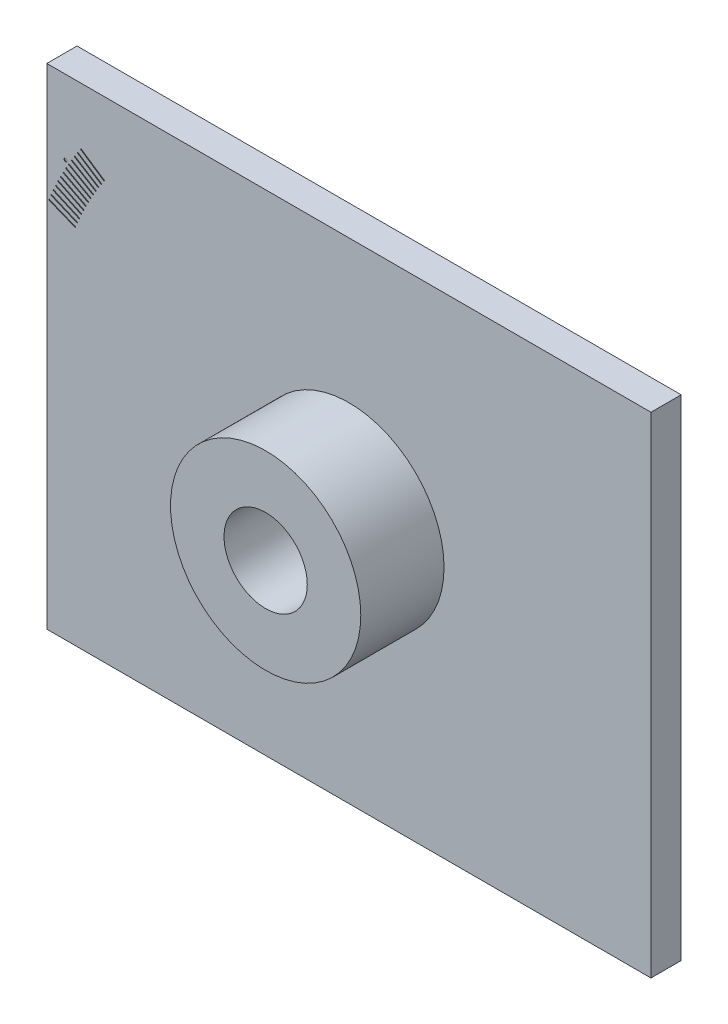
SolidWorks part; units mm, degrees
material "6063-T6"
ref_plane "Front Plane" through (0, 0, 0) normal (0, 0, 1) x (1, 0, 0)
ref_plane "Top Plane" through (0, 0, 0) normal (0, 1, 0) x (1, 0, 0)
ref_plane "Right Plane" through (0, 0, 0) normal (1, 0, 0) x (0, 0, -1)
sketch "Sketch1" plane through (0, 0, 0) normal (0, 0, 1) x (1, 0, 0)
  line L1 (-127, 100) -> (127, 100)
  line L2 (-127, 100) -> (-127, -106)
  line L3 (-127, -106) -> (127, -106)
  line L4 (127, 100) -> (127, -106)
  dimension "D1" = 127
  dimension "D2" = 127
  dimension "D3" = 100
  dimension "D4" = 106
extrude "Body" add sketch "Sketch1" along normal blind 12.7
sketch "Sketch2" plane through (0, 0, 12.7) normal (0, 0, 1) x (1, 0, 0)
  circle A0 centre (0, 0) radius 40
  dimension "D1" = 80
extrude "Spigot" add sketch "Sketch2" along normal blind 35
sketch "Sketch3" plane through (0, 0, 47.7) normal (0, 0, 1) x (1, 0, 0)
  circle A0 centre (0, 0) radius 17.5
  dimension "D1" = 35
extrude "Hole" cut sketch "Sketch3" against normal through all
sketch "Sketch4" plane through (0, 0, 12.7) normal (0, 0, 1) x (1, 0, 0)
  line L0 (0, 0) -> (-177.2977, 102.3629) construction
  line L1 (0, 0) -> (-190.234, 0) construction
  line L2 (0, 0) -> (-107.3872, 62)
  line L3 (-107.5122, 61.7835) -> (-107.2622, 62.2165)
  line L4 (-107.5122, 61.7835) -> (-117.9045, 67.7835)
  line L5 (-117.9045, 67.7835) -> (-117.6545, 68.2165)
  line L6 (-117.6545, 68.2165) -> (-107.2622, 62.2165)
  dimension "D1" = 30
  dimension "D2" = 124
  dimension "D3" = 0.5
  dimension "D4" = 12
extrude "Slit" cut sketch "Sketch4" against normal blind 0.25 contours L6 L5 L4 L3
sketch "Sketch5" plane through (0, 0, 12.7) normal (0, 0, 1) x (1, 0, 0)
  line L0 (0, 0) -> (-235.4142, 135.9165) construction
  line L1 (0, 0) -> (-227.8121, 0) construction
  dimension "D1" = 30
pattern_circular "Right Slits" count 5 every 1 about axis through (0, 0, 0) along (0, 0, 1) of "Slit"
pattern_circular "Left Slits" count 9 every 1 about axis through (0, 0, 0) along (0, 0, 1) of "Slit"
sketch "Sketch7" plane through (0, 0, 12.7) normal (0, 0, 1) x (1, 0, 0)
  line L0 (0, 0) -> (-235.4142, 135.9165) construction
  line L1 (-107.5122, 61.7835) -> (-107.2622, 62.2165) construction
  circle A0 centre (-119.0785, 68.75) radius 0.65
  dimension "D1" = 1.3
  dimension "D2" = 13.5
extrude "Tiny Hole" cut sketch "Sketch7" against normal blind 0.25
